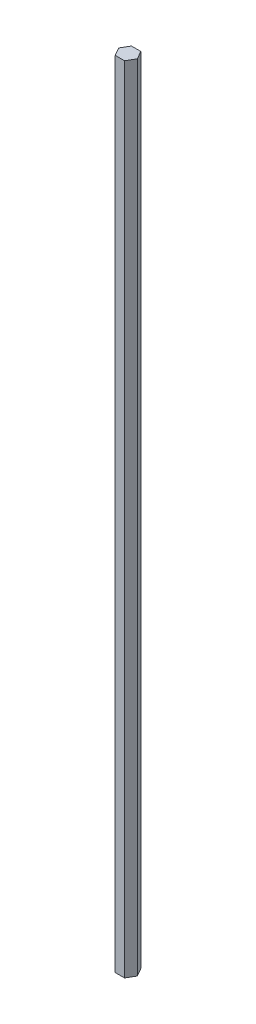
SolidWorks part; units mm, degrees
material "6061-T6 (SS)"
ref_plane "Front Plane" through (0, 0, 0) normal (0, 0, 1) x (1, 0, 0)
ref_plane "Top Plane" through (0, 0, 0) normal (0, 1, 0) x (1, 0, 0)
ref_plane "Right Plane" through (0, 0, 0) normal (1, 0, 0) x (0, 0, -1)
sketch "Sketch1" plane through (0, 0, 0) normal (0, 1, 0) x (1, 0, 0)
  line L1 (3.6662, -6.35) -> (7.3323, 0)
  line L2 (7.3323, 0) -> (3.6662, 6.35)
  line L3 (3.6662, 6.35) -> (-3.6662, 6.35)
  line L4 (-3.6662, 6.35) -> (-7.3323, 0)
  line L5 (-7.3323, 0) -> (-3.6662, -6.35)
  line L6 (-3.6662, -6.35) -> (3.6662, -6.35)
  circle A0 centre (0, 0) radius 6.35 construction
  dimension "D1" = 12.7
extrude "Boss-Extrude1" add sketch "Sketch1" along normal blind 622.3
